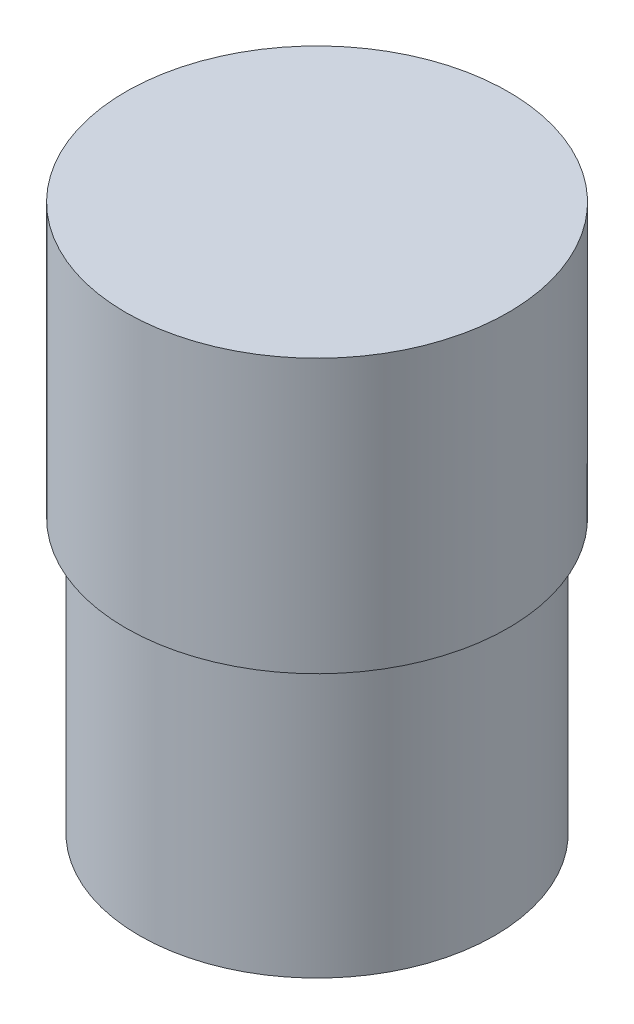
SolidWorks part; units mm, degrees
ref_plane "Front Plane" through (0, 0, 0) normal (0, 0, 1) x (1, 0, 0)
ref_plane "Top Plane" through (0, 0, 0) normal (0, 1, 0) x (1, 0, 0)
ref_plane "Right Plane" through (0, 0, 0) normal (1, 0, 0) x (0, 0, -1)
sketch "Sketch1" plane through (0, 0, 0) normal (0, 1, 0) x (1, 0, 0)
  circle A0 centre (0, 0) radius 41.275
  dimension "D1" = 82.55
extrude "Boss-Extrude1" add sketch "Sketch1" along normal blind 63.5
sketch "Sketch2" plane through (0, 63.5, 0) normal (0, 1, 0) x (1, 0, 0)
  circle A0 centre (0, 0) radius 44.45
  dimension "D1" = 88.9
extrude "Boss-Extrude2" add sketch "Sketch2" along normal blind 63.5
